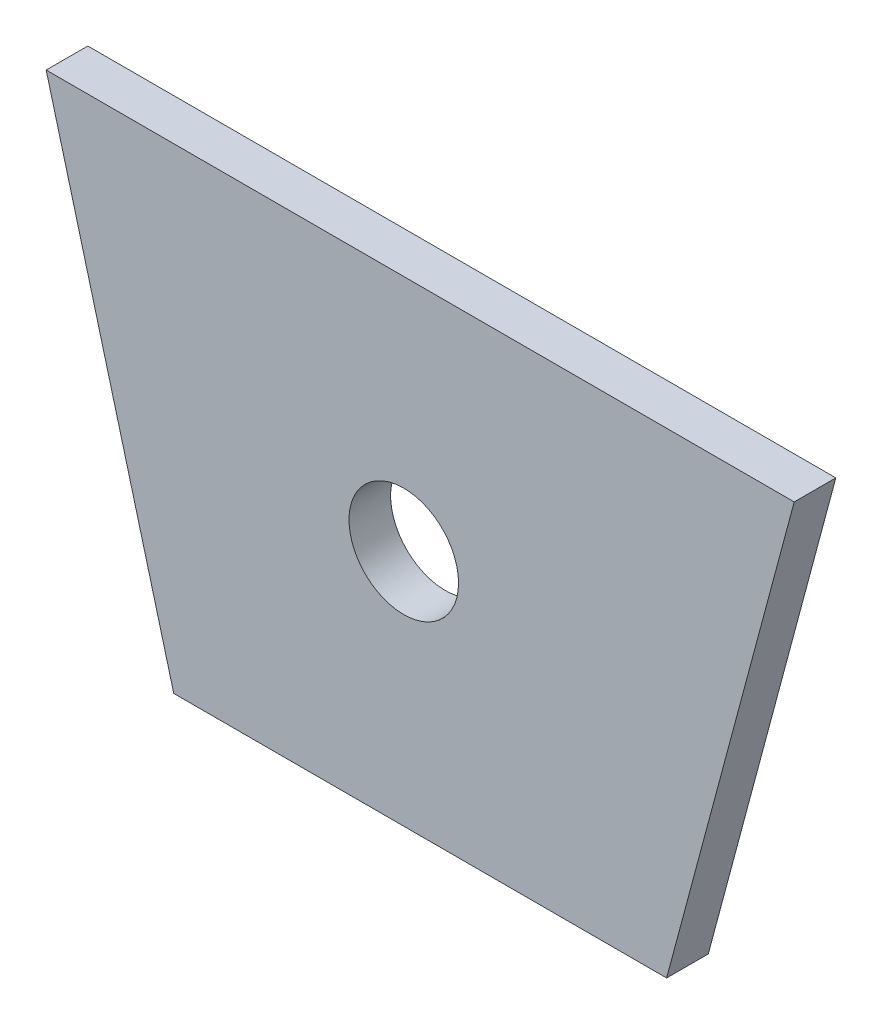
SolidWorks part; units mm, degrees
ref_plane "Front Plane" through (0, 0, 0) normal (0, 0, 1) x (1, 0, 0)
ref_plane "Top Plane" through (0, 0, 0) normal (0, 1, 0) x (1, 0, 0)
ref_plane "Right Plane" through (0, 0, 0) normal (1, 0, 0) x (0, 0, -1)
sketch "Sketch1" plane through (0, 0, 0) normal (0, 0, 1) x (1, 0, 0)
  line L0 (-26.67, -22.2118) -> (30.48, -22.2118)
  line L1 (-26.67, -22.2118) -> (-41.4615, 32.9909)
  line L2 (-41.4615, 32.9909) -> (45.2715, 32.9909)
  line L3 (45.2715, 32.9909) -> (30.48, -22.2118)
  line L4 (-26.67, -22.2118) -> (-26.67, 18.2788) construction
  line L5 (30.48, -22.2118) -> (30.48, 18.4871) construction
  line L6 (0, 0) -> (0, 157.312) construction
  line L7 (0, 0) -> (0, -410.2334) construction
  point P4 (0, 0)
  dimension "D1" = 57.15
  dimension "D2" = 57.15
  dimension "D3" = 15
  dimension "D4" = 15
extrude "Boss-Extrude1" add sketch "Sketch1" along normal blind 4.826
sketch "Sketch4" plane through (0, 0, 0) normal (0, 0, 1) x (1, 0, 0)
  circle A0 centre (0, 5.3895) radius 6.35
  point P2 (0, 5.3895)
  dimension "D1" = 12.7
extrude "Cut-Extrude5" cut sketch "Sketch4" along normal through all contours A0
